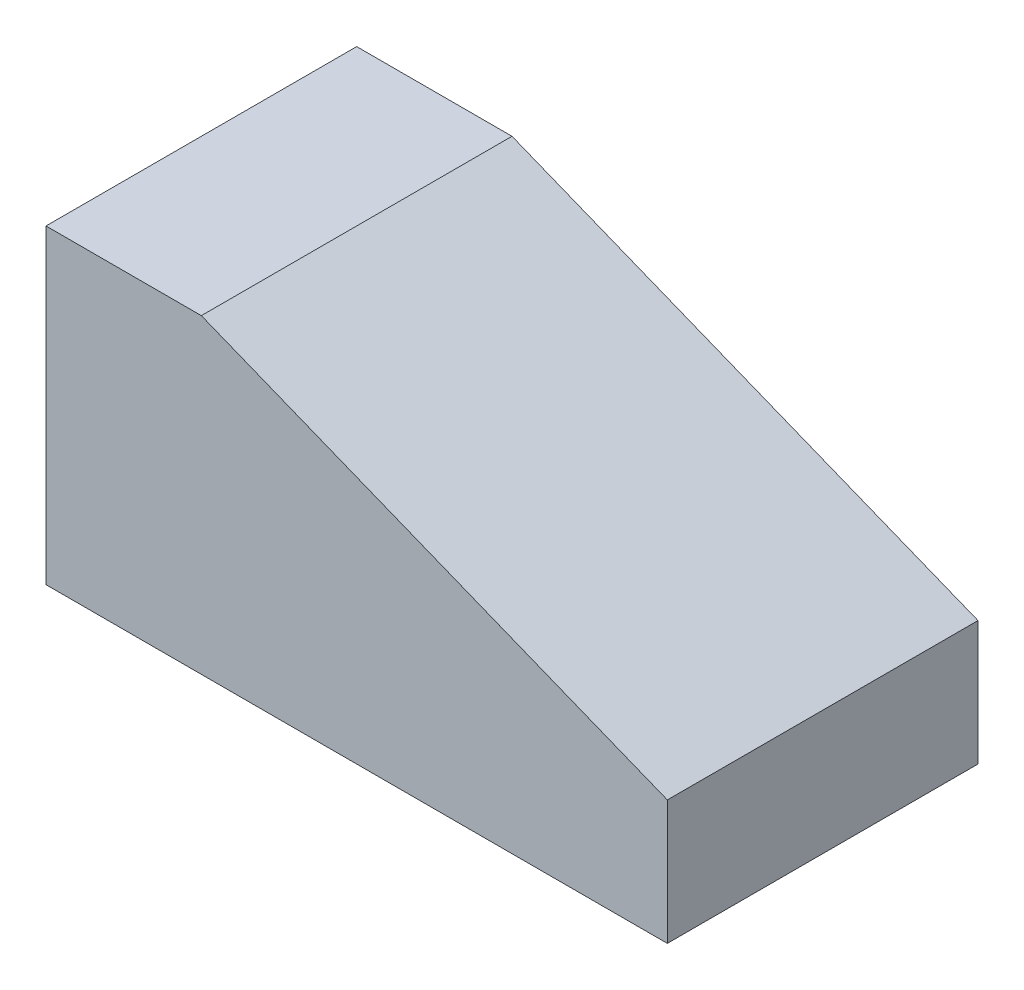
SolidWorks part; units mm, degrees
ref_plane "Front Plane" through (0, 0, 0) normal (0, 0, 1) x (1, 0, 0)
ref_plane "Top Plane" through (0, 0, 0) normal (0, 1, 0) x (1, 0, 0)
ref_plane "Right Plane" through (0, 0, 0) normal (1, 0, 0) x (0, 0, -1)
sketch "Sketch1" plane through (0, 0, 0) normal (0, 0, 1) x (1, 0, 0)
  line L0 (0, 0) -> (100, 0)
  line L1 (100, 0) -> (100, 20)
  line L2 (100, 20) -> (25, 50)
  line L3 (25, 50) -> (0, 50)
  line L4 (0, 50) -> (0, 0)
  dimension "D1" = 25
  dimension "D2" = 50
  dimension "D3" = 100
  dimension "D4" = 20
extrude "Boss-Extrude1" add sketch "Sketch1" along normal blind 50
